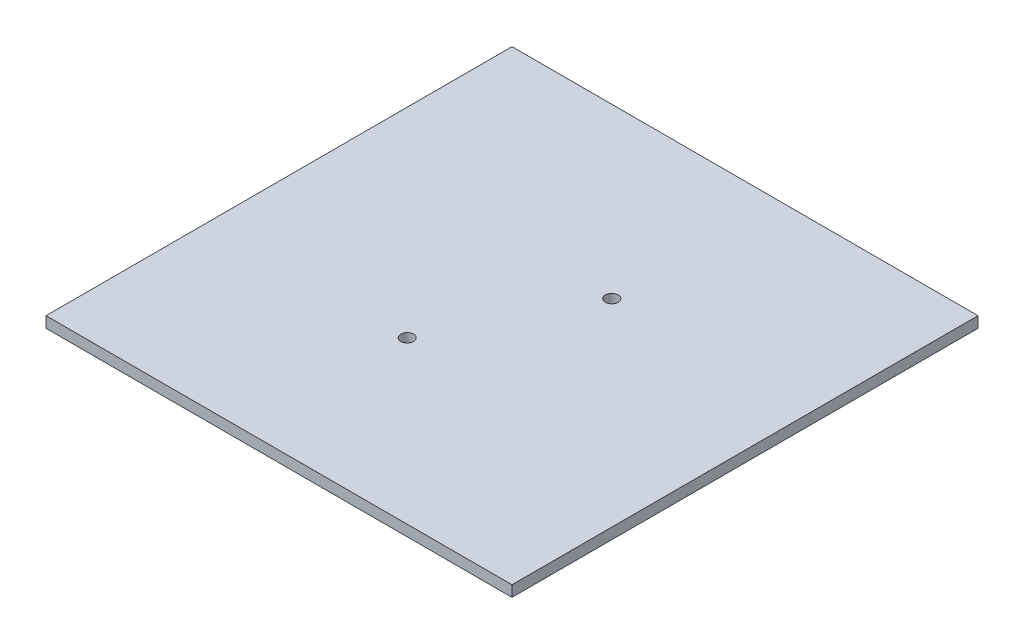
SolidWorks part; units mm, degrees
material "ABS"
ref_plane "Front Plane" through (0, 0, 0) normal (0, 0, 1) x (1, 0, 0)
ref_plane "Top Plane" through (0, 0, 0) normal (0, 1, 0) x (1, 0, 0)
ref_plane "Right Plane" through (0, 0, 0) normal (1, 0, 0) x (0, 0, -1)
sketch "Sketch1" plane through (0, 61.791, 0) normal (0, -1, 0) x (1, 0, 0)
  line L1 (-50.8, -50.8) -> (50.8, -50.8)
  line L2 (-50.8, -50.8) -> (-50.8, 50.8)
  line L3 (-50.8, 50.8) -> (50.8, 50.8)
  line L4 (50.8, -50.8) -> (50.8, 50.8)
  line L5 (-50.8, -50.8) -> (50.8, 50.8) construction
  line L6 (-50.8, 50.8) -> (50.8, -50.8) construction
  point P0 (0, 0)
  dimension "D1" = 101.6
  dimension "D2" = 101.6
extrude "Boss-Extrude1" add sketch "Sketch1" along normal blind 2.3813
hole_wizard "Ø2.5mm Dowel Hole1" positions "Sketch4" profile "Sketch5" hole size "Ø2.5" standard "ANSI Metric" end condition through all
sketch "Sketch4" plane through (0, 59.4097, 0) normal (0, -1, 0) x (-1, 0, 0)
  point P0 (7.25, -15.6)
  point P1 (-7.65, 14.1)
sketch "Sketch5" plane through (-7.25, 59.4097, 15.6) normal (1, 0, 0) x (0, 0, -1)
  line L0 (0, 0) -> (0, 2.3813)
  line L1 (0, 2.3813) -> (1.397, 2.3813)
  line L2 (1.397, 2.3813) -> (1.397, 0)
  line L3 (1.397, 0) -> (0, 0)
  line L4 (0, -6.35) -> (0, 107.95) construction
  dimension "Thru Hole Dia." = 2.794
  dimension "Thru Hole Depth" = 2.3813
